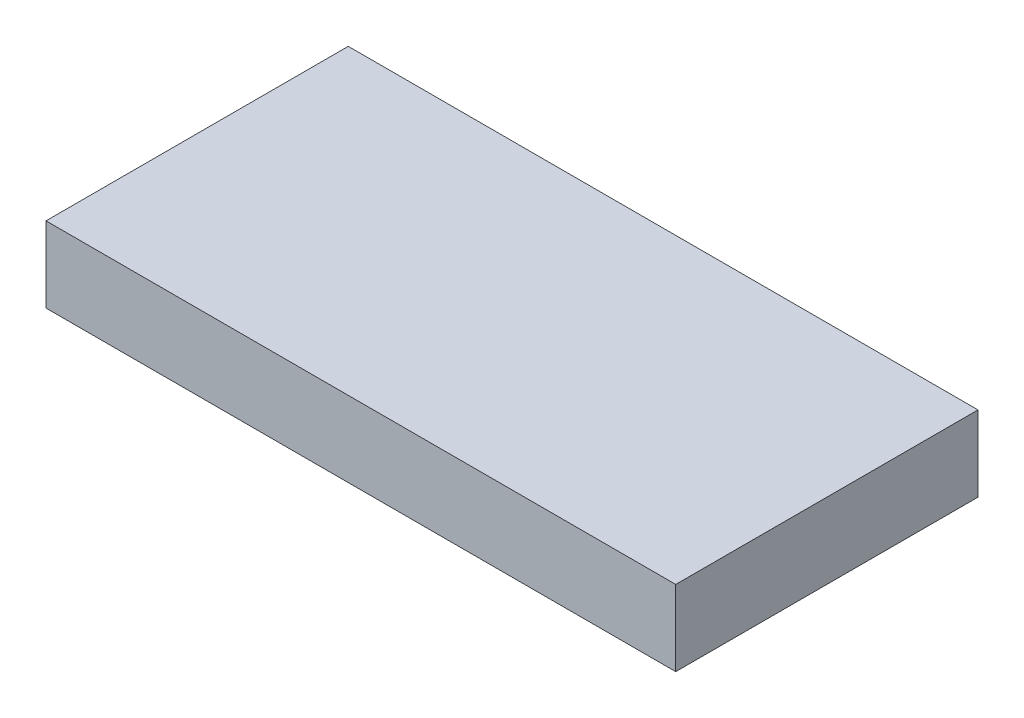
SolidWorks part; units mm, degrees
ref_plane "Front Plane" through (0, 0, 0) normal (0, 0, 1) x (1, 0, 0)
ref_plane "Top Plane" through (0, 0, 0) normal (0, 1, 0) x (1, 0, 0)
ref_plane "Right Plane" through (0, 0, 0) normal (1, 0, 0) x (0, 0, -1)
sketch "Sketch1" plane through (0, 0, 0) normal (0, 1, 0) x (1, 0, 0)
  line L1 (125, 60) -> (-125, 60)
  line L2 (125, 60) -> (125, -60)
  line L3 (125, -60) -> (-125, -60)
  line L4 (-125, 60) -> (-125, -60)
  line L5 (125, 60) -> (-125, -60) construction
  line L6 (125, -60) -> (-125, 60) construction
  point P0 (0, 0)
  dimension "D1" = 120
  dimension "D2" = 250
extrude "Boss-Extrude1" add sketch "Sketch1" along normal blind 30
